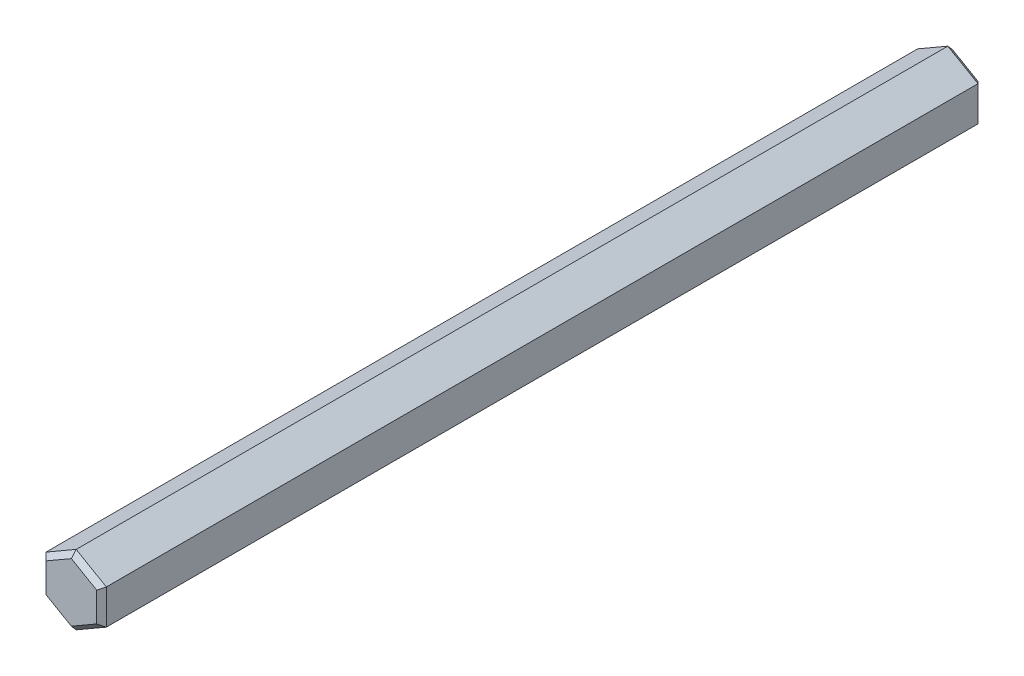
SolidWorks part; units mm, degrees
material "Plain Carbon Steel"
ref_plane "Front Plane" through (0, 0, 0) normal (0, 0, 1) x (1, 0, 0)
ref_plane "Top Plane" through (0, 0, 0) normal (0, 1, 0) x (1, 0, 0)
ref_plane "Right Plane" through (0, 0, 0) normal (1, 0, 0) x (0, 0, -1)
ref_plane "Plane1" through (0, 0, 75) normal (0, 0, 1) x (1, 0, 0)
sketch "Sketch1" plane through (0, 0, 75) normal (0, 0, 1) x (1, 0, 0)
  line L0 (0, -2.8868) -> (2.5, -1.4434)
  line L1 (2.5, -1.4434) -> (2.5, 1.4434)
  line L2 (2.5, 1.4434) -> (0, 2.8868)
  line L3 (0, 2.8868) -> (-2.5, 1.4434)
  line L4 (-2.5, 1.4434) -> (-2.5, -1.4434)
  line L5 (-2.5, -1.4434) -> (0, -2.8868)
extrude "Boss-Extrude1" add sketch "Sketch1" against normal blind 73.025
chamfer "Chamfer1" distance 0.4 angle 45 12 edges at (-2.5, 0, 1.975) (-1.25, -2.1651, 1.975) (-1.25, 2.1651, 1.975) (1.25, -2.1651, 1.975) (1.25, 2.1651, 1.975) (2.5, 0, 1.975) (-1.25, 2.1651, 75) (-2.5, 0, 75) (1.25, 2.1651, 75) (-1.25, -2.1651, 75) (2.5, 0, 75) (1.25, -2.1651, 75)
